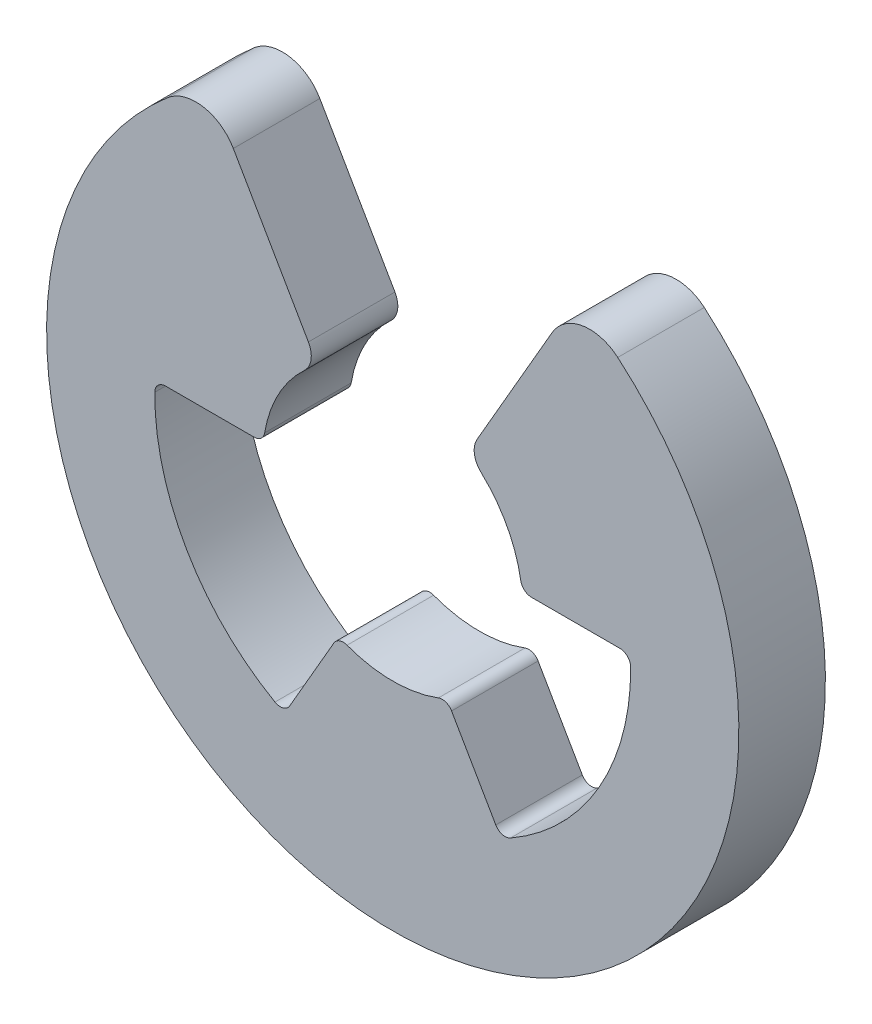
SolidWorks part; units mm, degrees
material "Plain Carbon Steel"
ref_plane "Front Plane" through (0, 0, 0) normal (0, 0, 1) x (1, 0, 0)
ref_plane "Top Plane" through (0, 0, 0) normal (0, 1, 0) x (1, 0, 0)
ref_plane "Right Plane" through (0, 0, 0) normal (1, 0, 0) x (0, 0, -1)
sketch "Sketch2" plane through (0, 0, 0) normal (0, 0, 1) x (1, 0, 0)
  line L0 (0, -3) -> (0, -8) construction
  line L1 (-2.5981, 1.5) -> (-6.9282, 4) construction
  line L2 (0, 0) -> (6.9282, 4) construction
  line L3 (2.3816, -4.6871) -> (1.3598, -2.9173)
  line L4 (-2.3816, -4.6871) -> (-1.3598, -2.9173)
  line L5 (-2.9898, 4.6164) -> (-1.9493, 2.8141)
  line L6 (-5.2499, 0.2811) -> (-3.2063, 0.2811)
  line L7 (5.2499, 0.2811) -> (3.2063, 0.2811)
  line L8 (2.9898, 4.6164) -> (1.9493, 2.8141)
  line L9 (-2.9898, 4.6164) -> (-3.6843, 5.8193)
  line L10 (2.9898, 4.6164) -> (3.6843, 5.8193)
  arc A0 (-5.2004, 6.0792) -> (5.2004, 6.0792) centre (0, 0) ccw
  arc A1 (-5.4999, 0.0325) -> (-2.7218, -4.7793) centre (0, 0) ccw
  arc A2 (-2.042, 2.1978) -> (-2.9597, 0.4902) centre (0, 0) ccw
  arc A3 (-1.0553, -2.8083) -> (1.0553, -2.8083) centre (0, 0) ccw
  arc A4 (2.9597, 0.4902) -> (2.042, 2.1978) centre (0, 0) ccw
  arc A5 (2.7218, -4.7793) -> (5.4999, 0.0325) centre (0, 0) ccw
  arc A6 (5.4999, 0.0325) -> (5.2499, 0.2811) centre (5.2499, 0.0311) ccw
  arc A7 (2.7218, -4.7793) -> (2.3816, -4.6871) centre (2.5981, -4.5621) cw
  arc A8 (-2.7218, -4.7793) -> (-2.3816, -4.6871) centre (-2.5981, -4.5621) ccw
  arc A9 (-5.4999, 0.0325) -> (-5.2499, 0.2811) centre (-5.2499, 0.0311) cw
  arc A10 (-3.2063, 0.2811) -> (-2.9597, 0.4902) centre (-3.2063, 0.5311) ccw
  arc A11 (2.9597, 0.4902) -> (3.2063, 0.2811) centre (3.2063, 0.5311) ccw
  arc A12 (1.3598, -2.9173) -> (1.0553, -2.8083) centre (1.1433, -3.0423) ccw
  arc A13 (-1.3598, -2.9173) -> (-1.0553, -2.8083) centre (-1.1433, -3.0423) cw
  arc A14 (1.9493, 2.8141) -> (2.042, 2.1978) centre (2.3823, 2.5641) ccw
  arc A15 (-1.9493, 2.8141) -> (-2.042, 2.1978) centre (-2.3823, 2.5641) cw
  arc A16 (5.2004, 6.0792) -> (3.6843, 5.8193) centre (4.5503, 5.3193) ccw
  arc A17 (-3.6843, 5.8193) -> (-5.2004, 6.0792) centre (-4.5503, 5.3193) ccw
  point P9 (0, 0)
  point P23 (0, 0)
  point P27 (2.503, -4.8974)
  point P30 (-2.503, -4.8974)
  point P39 (1.25, -2.7272)
  point P42 (-1.25, -2.7272)
  dimension "D1" = 16
  dimension "D3" = 6
  dimension "D4" = 2.5
  dimension "D8" = 0.25
  dimension "D9" = 0.25
  dimension "D10" = 0.5
  dimension "D11" = 1
  dimension "D5" = 30
  dimension "D6" = 1.25
  dimension "D2" = 3
  dimension "D7" = 3
extrude "Boss-Extrude1" add sketch "Sketch2" along normal blind 2
